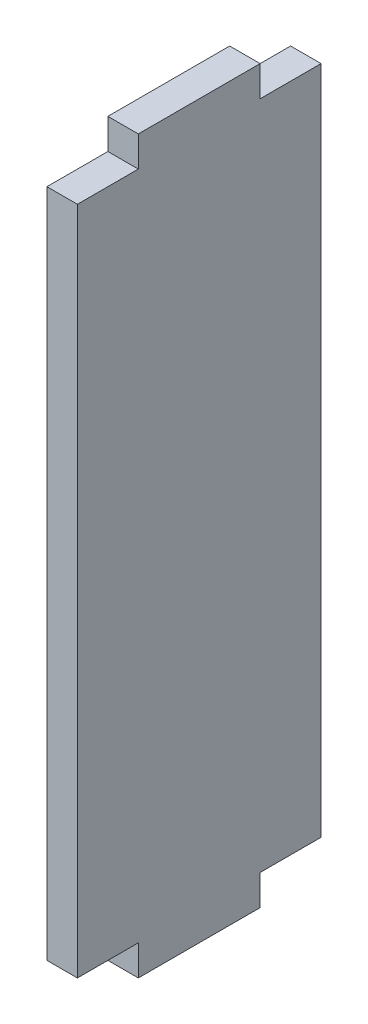
SolidWorks part; units mm, degrees
ref_plane "Front Plane" through (0, 0, 0) normal (0, 0, 1) x (1, 0, 0)
ref_plane "Top Plane" through (0, 0, 0) normal (0, 1, 0) x (1, 0, 0)
ref_plane "Right Plane" through (0, 0, 0) normal (1, 0, 0) x (0, 0, -1)
sketch "Sketch1" plane through (0, 0, 0) normal (1, 0, 0) x (0, 0, -1)
  line L0 (-43.807, 0) -> (-20, 0) construction
  line L1 (-20, 45) -> (-10, 45)
  line L2 (-20, 45) -> (-20, -65)
  line L3 (-20, -65) -> (-10, -65)
  line L4 (20, 45) -> (20, -65)
  line L7 (0, 51.3264) -> (0, 50) construction
  line L8 (-10, 45) -> (-10, 50)
  line L9 (-10, 50) -> (10, 50)
  line L10 (10, 50) -> (10, 45)
  line L11 (10, -65) -> (10, -70)
  line L12 (10, -70) -> (-10, -70)
  line L13 (-10, -70) -> (-10, -65)
  line L14 (10, 45) -> (20, 45)
  line L16 (10, -65) -> (20, -65)
  line L17 (0, -70) -> (0, -82.073) construction
  line L18 (20, 0) -> (37.0281, 0) construction
  point P0 (0, 0)
  dimension "D1" = 110
  dimension "D2" = 40
  dimension "D3" = 20
  dimension "D4" = 5
  dimension "D5" = 20
  dimension "D6" = 5
extrude "Boss-Extrude1" add sketch "Sketch1" along normal blind 5
